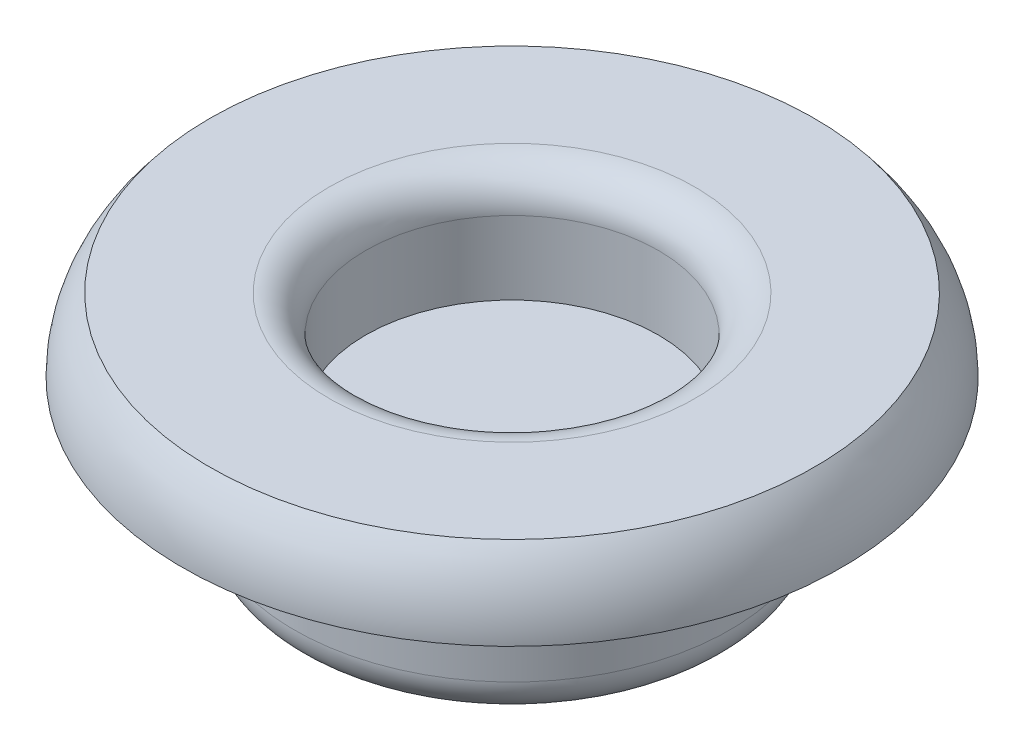
SolidWorks part; units mm, degrees
material "ABS"
ref_plane "Front Plane" through (0, 0, 0) normal (0, 0, 1) x (1, 0, 0)
ref_plane "Top Plane" through (0, 0, 0) normal (0, 1, 0) x (1, 0, 0)
ref_plane "Right Plane" through (0, 0, 0) normal (1, 0, 0) x (0, 0, -1)
sketch "Sketch1" plane through (0, 0, 0) normal (0, 0, 1) x (1, 0, 0)
  line L0 (0, 0) -> (0, -6) construction
  line L1 (0, -6) -> (4.95, -6)
  line L2 (5.95, -5) -> (5.95, -2)
  line L3 (5.95, -2) -> (9, -2)
  line L5 (8.2527, 0) -> (5, 0)
  line L6 (4, -1) -> (4, -3)
  line L7 (4, -3) -> (0, -3)
  line L8 (0, -3) -> (0, -6)
  arc A0 (9, -2) -> (8.2527, 0) centre (5.95, -2) ccw
  arc A1 (5, 0) -> (4, -1) centre (5, -1) ccw
  arc A2 (4.95, -6) -> (5.95, -5) centre (4.95, -5) ccw
  point P6 (0, 0)
  dimension "D6" = 1
  dimension "D8" = 1
  dimension "D1" = 3
  dimension "D2" = 2
  dimension "D3" = 4
  dimension "D4" = 5.95
  dimension "D5" = 6
  dimension "D7" = 9
revolve "Revolve1" add sketch "Sketch1" angle 360 about L0
